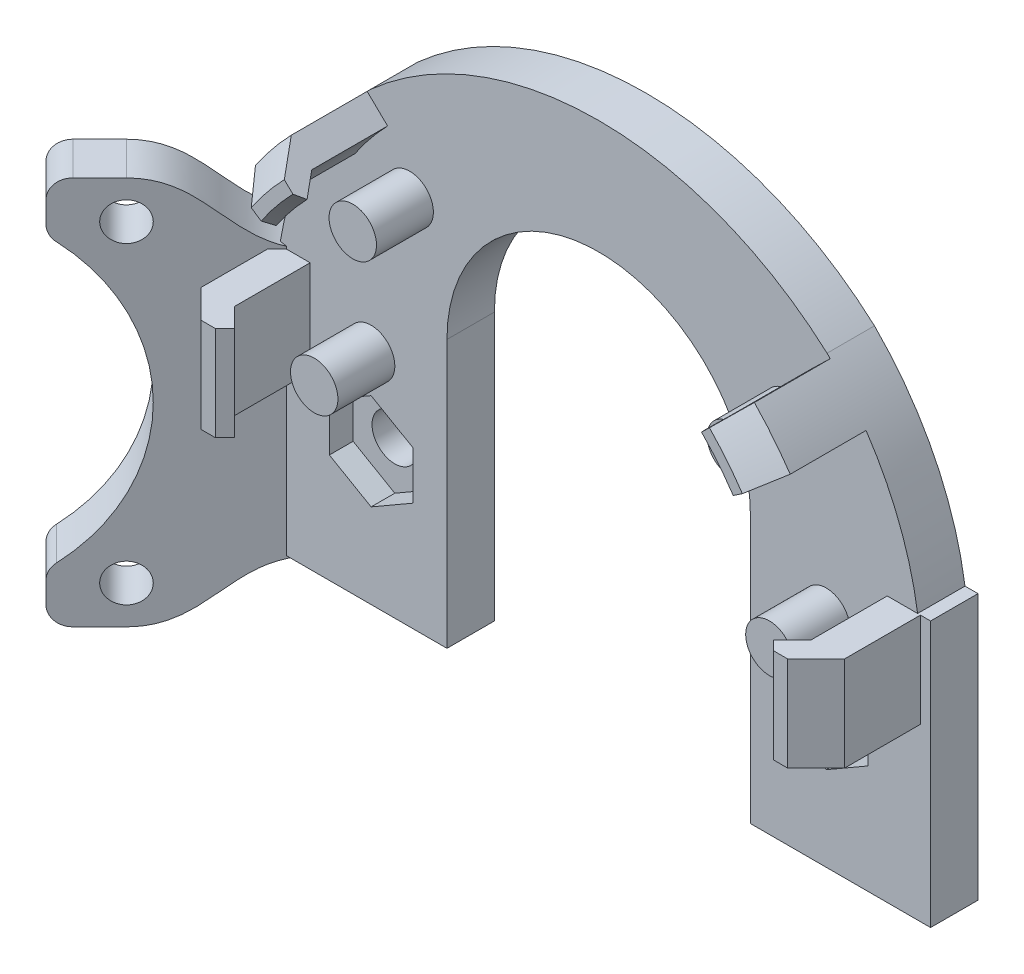
SolidWorks part; units mm, degrees
ref_plane "Front" through (0, 0, 0) normal (0, 0, 1) x (1, 0, 0)
ref_plane "Top" through (0, 0, 0) normal (0, 1, 0) x (1, 0, 0)
ref_plane "Right" through (0, 0, 0) normal (1, 0, 0) x (0, 0, -1)
sketch "Sketch2" plane through (0, 0, 0) normal (0, 0, 1) x (1, 0, 0)
  line L1 (-35, -14) -> (35, -14)
  line L2 (-35, -14) -> (-35, 14)
  line L3 (-35, 14) -> (35, 14)
  line L4 (35, -14) -> (35, 14)
  line L5 (-35, -14) -> (35, 14) construction
  line L6 (-35, 14) -> (35, -14) construction
  point P0 (0, 0)
  dimension "D1" = 28
  dimension "D2" = 70
extrude "Boss-Extrude1" add sketch "Sketch2" along normal blind 5
sketch "Sketch3" plane through (0, 0, 5) normal (0, 0, 1) x (1, 0, 0)
  line L1 (28.4, 2.5403) -> (24, 5.0807)
  line L2 (24, 5.0807) -> (19.6, 2.5403)
  line L3 (19.6, 2.5403) -> (19.6, -2.5403)
  line L4 (19.6, -2.5403) -> (24, -5.0807)
  line L5 (24, -5.0807) -> (28.4, -2.5403)
  line L6 (28.4, -2.5403) -> (28.4, 2.5403)
  circle A0 centre (24, 0) radius 4.4 construction
  dimension "D1" = 8.8
  dimension "D2" = 24
extrude "Cut-Nut" cut sketch "Sketch3" against normal blind 2.5
sketch "Sketch4" plane through (0, 0, 2.5) normal (0, 0, 1) x (1, 0, 0)
  circle A0 centre (24, 0) radius 2.4
  dimension "D1" = 4.8
extrude "Cut-Screw" cut sketch "Sketch4" against normal through all
mirror "Mirror1" about plane through (0, 0, 0) normal (1, 0, 0) of "Cut-Screw", "Cut-Nut"
ref_plane "Plane1" through (-17.5, 0, -17.5) normal (-0.7071, 0, -0.7071) x (-0.7071, 0, 0.7071)
sketch "Sketch8" plane through (0, 0, 5) normal (0, 0, 1) x (1, 0, 0)
  circle A0 centre (0, 0) radius 11
  dimension "D1" = 22
extrude "Cut-Hot End" cut sketch "Sketch8" against normal through all
sketch "Sketch11" plane through (0, 0, 5) normal (0, 0, 1) x (1, 0, 0)
  line L1 (-11, -14) -> (11, -14)
  line L2 (-11, -14) -> (-11, 0)
  line L3 (-11, 0) -> (11, 0)
  line L4 (11, -14) -> (11, 0)
  line L5 (-35, -14) -> (35, -14) construction
  circle A0 centre (0, 0) radius 11 construction
extrude "Cut-Extrude8" cut sketch "Sketch11" against normal through all
sketch "Sketch6" plane through (-17.5, 0, -17.5) normal (-0.7071, 0, -0.7071) x (-0.7071, 0, 0.7071)
  line L0 (38.7487, 16.5) -> (38.7487, -16.5) construction
  line L2 (-21.2132, 14) -> (28.2843, 14) construction
  line L3 (38.7487, 20.5) -> (44.7487, 20.5)
  line L4 (38.7487, 20.5) -> (24.7487, 14) construction
  line L5 (38.7487, 0) -> (0, 0) construction
  line L6 (44.7487, 20.5) -> (44.7487, -20.5)
  line L7 (38.7487, -20.5) -> (44.7487, -20.5)
  line L8 (24.7487, 14) -> (24.7487, -14)
  line L9 (24.7487, 14) -> (24.7487, -14) construction
  spline S0 degree 3 poles (24.7487, 14) (30.9714, 14) (32.5261, 20.5) (38.7487, 20.5) knots 0 0 0 0 1 1 1 1
  spline S1 degree 3 poles (24.7487, -14) (30.9714, -14) (32.5261, -20.5) (38.7487, -20.5) knots 0 0 0 0 1 1 1 1
  point P2 (38.7487, 0)
  dimension "D1" = 33
  dimension "D2" = 14
  dimension "D3" = 4
  dimension "D4" = 6
extrude "Boss-Fan" add sketch "Sketch6" against normal blind 5
sketch "Sketch9" plane through (-17.5, 0, -17.5) normal (-0.7071, 0, -0.7071) x (-0.7071, 0, 0.7071)
  line L1 (44.7487, -20.5) -> (44.7487, 20.5) construction
  circle A0 centre (38.7487, 16.5) radius 2
  dimension "D1" = 4
  dimension "D2" = 16.5
  dimension "D3" = 6
extrude "Cut-Fan Screw" cut sketch "Sketch9" against normal through all
mirror "Mirror-Fan Screw" about plane through (0, 0, 0) normal (0, 1, 0) of "Cut-Fan Screw"
sketch "Sketch10" plane through (-17.5, 0, -17.5) normal (-0.7071, 0, -0.7071) x (-0.7071, 0, 0.7071)
  line L0 (36.7487, 23.5316) -> (36.7487, -27.9587) construction
  line L1 (36.7487, 16.5) -> (36.7487, -16.5) construction
  circle A0 centre (55.2487, 0) radius 18.5
  circle A1 centre (38.7487, 16.5) radius 2 construction
  circle A2 centre (38.7487, -16.5) radius 2 construction
  dimension "D1" = 37
extrude "Cut-Extrude7" cut sketch "Sketch10" against normal through all
fillet "Fillet2" radius 2 4 edges at (-47.3744, -20.5, 15.9099) (-47.3744, 15.2315, 15.9099) (-47.3744, -15.2315, 15.9099) (-47.3744, 20.5, 15.9099)
sketch "Sketch12" plane through (0, 0, 5) normal (0, 0, 1) x (1, 0, 0)
  line L1 (-33.9289, 14) -> (-30.4289, 14)
  line L2 (-33.9289, 14) -> (-33.9289, 4.0275)
  line L3 (-33.9289, 4.0275) -> (-30.4289, 4.0275)
  line L4 (-30.4289, 14) -> (-30.4289, 4.0275)
  line L6 (35, 14) -> (-32.9289, 14) construction
  line L7 (-32.9289, 14) -> (-32.9289, -14) construction
  dimension "D1" = 3.5
  dimension "D2" = 2.5
extrude "Boss-Back Hook" add sketch "Sketch12" along normal blind 8
sketch "Sketch14" plane through (0, 4.0275, 0) normal (0, -1, 0) x (1, 0, 0)
  line L0 (-30.4289, 13) -> (-28.4289, 15)
  line L1 (-28.4289, 15) -> (-29.4289, 16)
  line L2 (-29.4289, 16) -> (-30.9289, 16)
  line L3 (-30.9289, 16) -> (-33.9289, 13)
  line L4 (-33.9289, 13) -> (-30.4289, 13) construction
  line L5 (-33.9289, 13) -> (-30.4289, 13)
  dimension "D1" = 45
  dimension "D2" = 1.5
  dimension "D3" = 2
extrude "Boss-Back Hook Top" add sketch "Sketch14" against normal up to surface (9.9725 mm away) up to face at (-15.6475, 14, 5.6919)
sketch "Sketch17" plane through (0, 0, 5) normal (0, 0, 1) x (1, 0, 0)
  line L1 (-28.4289, 9.0138) -> (-6.3049, 9.0138) construction
  line L2 (-28.4289, 14) -> (-28.4289, 4.0275) construction
  line L3 (-24, 0) -> (-24, 9.0138) construction
  line L6 (0, 0) -> (0, 14) construction
  line L7 (35, 14) -> (-30.4289, 14) construction
  circle A0 centre (-24, 9.0138) radius 2.5
  arc A1 (11, 0) -> (-11, 0) centre (0, 0) ccw construction
  circle A3 centre (24, 9.0138) radius 2.5
  dimension "D1" = 5
mirror "Mirror-Back Hook" about plane through (0, 0, 0) normal (1, 0, 0) of "Boss-Back Hook Top", "Boss-Back Hook"
fillet "Fillet3" [suppressed] radius 3
extrude "Boss-Extrude10" add sketch "Sketch17" along normal blind 6
sketch "Sketch20" plane through (0, 0, 0) normal (0, 0, -1) x (-1, 0, 0)
  line L1 (-35, 14) -> (35, 14) construction
  line L2 (24.0832, 33) -> (15.5832, 24.5294)
  line L3 (21.4243, 14) -> (33.6303, 14)
  line L6 (-35, 14) -> (35, 14) construction
  arc A0 (33.6303, 14) -> (24.0832, 33) centre (0, 9) ccw
  arc A1 (21.4243, 14) -> (15.5832, 24.5294) centre (0, 9) ccw
  dimension "D1" = 34
  dimension "D4" = 9
  dimension "D2" = 19
  dimension "D3" = 12
extrude "Boss-Front Support" add sketch "Sketch20" against normal up to surface (5 mm away) up to face at (-26.5, 9.0138, 5)
sketch "Sketch21" plane through (0, 0, 5) normal (0, 0, 1) x (1, 0, 0)
  line L1 (-24.4168, 32.6605) -> (-22.2624, 30.5728)
  line L2 (-25.7079, 26.3235) -> (-28.1957, 28)
  line L4 (30.4289, 14) -> (-21.4243, 14) construction
  arc A0 (-24.4168, 32.6605) -> (-28.1957, 28) centre (0, 9) ccw
  arc A1 (-24.0832, 33) -> (-33.5689, 14.3972) centre (0, 9) ccw construction
  arc A2 (-22.2624, 30.5728) -> (-25.7079, 26.3235) centre (0, 9) ccw
  arc A3 (-24.4168, 32.6605) -> (-28.1957, 28) centre (0, 9) ccw construction
  dimension "D1" = 6
  dimension "D2" = 3
  dimension "D3" = 14
extrude "Boss-Front Hook" add sketch "Sketch21" along normal up to vertex (8 mm away)
sketch "Sketch22" plane through (4.7524, 4.3948, 0) normal (0.6959, 0.7181, 0) x (0, 0, -1)
  line L0 (-13, 37.6176) -> (-13, 40.6176)
  line L1 (-13, 37.6176) -> (-13, 40.6176) construction
  line L2 (-13, 40.6176) -> (-15.6117, 38.006)
  line L3 (-15.6117, 38.006) -> (-15.6117, 36.7471)
  line L4 (-15.6117, 36.7471) -> (-14.7411, 35.8765)
  line L5 (-14.7411, 35.8765) -> (-13, 37.6176)
  line L6 (-15, 30.5132) -> (-13, 31.9494) construction
  line L7 (-16, 31.2313) -> (-15, 30.5132) construction
  dimension "D1" = 45
sweep "Sweep-Front Hook Top" add profiles "Sketch22" path edge at (-24.0791, 28.5243, 13)
sketch "Sketch25" plane through (0, 0, 5) normal (0, 0, 1) x (1, 0, 0)
  line L0 (-22.7267, 27.4277) -> (-17.1378, 22.7948) construction
  circle A0 centre (-19.9322, 25.1112) radius 2.5
  arc A1 (-21.0121, 29.3611) -> (-24.264, 25.3506) centre (0, 9) ccw construction
  arc A2 (-15.5832, 24.5294) -> (-21.4243, 14) centre (0, 9) ccw construction
  dimension "D1" = 5
extrude "Boss-Front Pin" add sketch "Sketch25" along normal up to surface (6 mm away) up to face at (-21.5, 9.0138, 11)
sketch "Sketch23" plane through (0, 0, 0) normal (0, 0, -1) x (-1, 0, 0)
  line L1 (0, 42.2134) -> (0, 14)
  line L2 (0, 14) -> (33.6303, 14)
  line L4 (-35, 14) -> (21.4243, 14) construction
  line L5 (0, 42.2134) -> (-15.5737, 42.2134) construction
  line L6 (24.0832, 33) -> (33.6303, 14)
  arc A0 (0, 42.2134) -> (24.0832, 33) centre (0, 6.1306) cw
extrude "Boss-Front Curve" add sketch "Sketch23" against normal up to surface (5 mm away) up to face at (-7.9312, 10.8152, 5)
mirror "Mirror5" about plane through (0, 0, 0) normal (1, 0, 0) of "Boss-Front Pin", "Boss-Front Hook", "Boss-Front Support", "Boss-Front Curve"
sketch "Sketch24" plane through (-4.1708, 6.1894, 0) normal (0.5588, -0.8293, 0) x (0.8293, 0.5588, 0)
  line L0 (36.0294, 13) -> (39.0294, 13)
  line L1 (39.0294, 13) -> (36.2736, 15.7559)
  line L2 (36.2736, 15.7559) -> (35.1108, 15.7559)
  line L3 (35.1108, 15.7559) -> (34.1922, 14.8372)
  line L4 (34.1922, 14.8372) -> (36.0294, 13)
  line L7 (35.9603, 13) -> (33.4725, 16) construction
  line L9 (32.2285, 16) -> (31.3993, 15) construction
  line L11 (31.3993, 15) -> (33.0578, 13) construction
  dimension "D1" = 45
sweep "Sweep2" add profiles "Sketch24" path edge at (24.0791, 28.5243, 13)
sketch "Sketch26" plane through (0, 0, 0) normal (0, 0, -1) x (-1, 0, 0)
  line L0 (-16, -14) -> (-16, 14.2134)
  line L1 (-11, -14) -> (-35, -14) construction
  line L2 (0, 30.2134) -> (22.021, 30.2134) construction
  line L3 (-16, -14) -> (16, -14)
  line L4 (0, -14) -> (0, 30.2134) construction
  line L5 (16, -14) -> (16, 14.2134)
  arc A0 (-16, 14.2134) -> (16, 14.2134) centre (0, 14.2134) cw
  arc A1 (24.0832, 33) -> (-24.0832, 33) centre (0, 6.1306) ccw construction
  point P13 (0, 42.2134)
  dimension "D1" = 12
  dimension "D2" = 16
extrude "Cut-Extrude9" cut sketch "Sketch26" against normal through all
